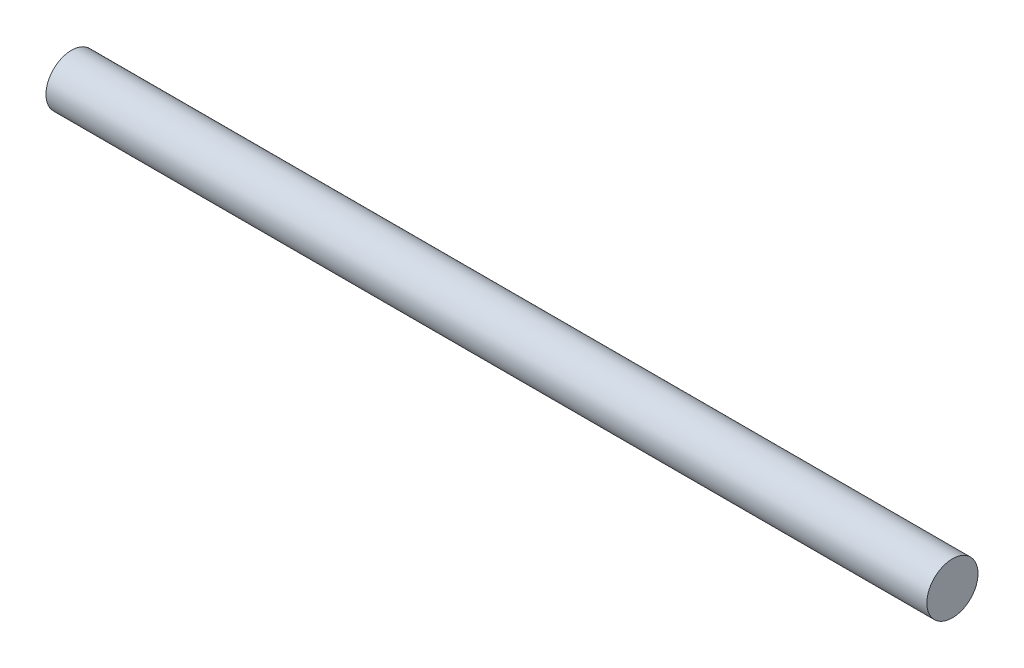
SolidWorks part; units mm, degrees
ref_plane "Plan de face" through (0, 0, 0) normal (0, 0, 1) x (1, 0, 0)
ref_plane "Plan de dessus" through (0, 0, 0) normal (0, 1, 0) x (1, 0, 0)
ref_plane "Plan de droite" through (0, 0, 0) normal (1, 0, 0) x (0, 0, -1)
sketch "Esquisse5" plane through (0, 0, 0) normal (1, 0, 0) x (0, 0, -1)
  circle A0 centre (0, 0) radius 18
extrude "Boss.-Extru.3" add sketch "Esquisse5" along normal blind 620
ref_plane "Plan2" through (10, 0, 0) normal (-1, 0, 0) x (0, 0, 1)
ref_plane "Plan4" through (610, 0, 0) normal (-1, 0, 0) x (0, 0, 1)
sketch "Esquisse6" plane through (10, 0, 0) normal (-1, 0, 0) x (0, 0, 1)
  circle A0 centre (0, 0) radius 18
sketch "Esquisse7" plane through (610, 0, 0) normal (-1, 0, 0) x (0, 0, 1)
  circle A0 centre (0, 0) radius 18
ref_plane "Plan31" through (590, 0, 0) normal (-1, 0, 0) x (0, 0, 1)
sketch "Esquisse32" plane through (590, 0, 0) normal (-1, 0, 0) x (0, 0, 1)
  circle A0 centre (0, 0) radius 18
ref_plane "Plan32" through (530, 0, 0) normal (-1, 0, 0) x (0, 0, 1)
sketch "Esquisse38" plane through (530, 0, 0) normal (-1, 0, 0) x (0, 0, 1)
  circle A0 centre (0, 0) radius 18
ref_plane "Plan39" through (450, 0, 0) normal (-1, 0, 0) x (0, 0, 1)
sketch "Esquisse42" plane through (450, 0, 0) normal (-1, 0, 0) x (0, 0, 1)
  circle A0 centre (0, 0) radius 18
ref_plane "Plan40" through (350, 0, 0) normal (-1, 0, 0) x (0, 0, 1)
ref_plane "Plan41" through (330, 0, 0) normal (-1, 0, 0) x (0, 0, 1)
ref_plane "Plan42" through (290, 0, 0) normal (-1, 0, 0) x (0, 0, 1)
ref_plane "Plan43" through (270, 0, 0) normal (-1, 0, 0) x (0, 0, 1)
ref_plane "Plan44" through (170, 0, 0) normal (-1, 0, 0) x (0, 0, 1)
ref_plane "Plan45" through (90, 0, 0) normal (-1, 0, 0) x (0, 0, 1)
ref_plane "Plan46" through (30, 0, 0) normal (-1, 0, 0) x (0, 0, 1)
sketch "Esquisse43" plane through (350, 0, 0) normal (-1, 0, 0) x (0, 0, 1)
  circle A0 centre (0, 0) radius 18
sketch "Esquisse44" plane through (330, 0, 0) normal (-1, 0, 0) x (0, 0, 1)
  circle A0 centre (0, 0) radius 18
sketch "Esquisse45" plane through (290, 0, 0) normal (-1, 0, 0) x (0, 0, 1)
  circle A0 centre (0, 0) radius 18
sketch "Esquisse46" plane through (270, 0, 0) normal (-1, 0, 0) x (0, 0, 1)
  circle A0 centre (0, 0) radius 18
sketch "Esquisse47" plane through (170, 0, 0) normal (-1, 0, 0) x (0, 0, 1)
  circle A0 centre (0, 0) radius 18
sketch "Esquisse48" plane through (90, 0, 0) normal (-1, 0, 0) x (0, 0, 1)
  circle A0 centre (0, 0) radius 18
sketch "Esquisse49" plane through (30, 0, 0) normal (-1, 0, 0) x (0, 0, 1)
  circle A0 centre (0, 0) radius 18
